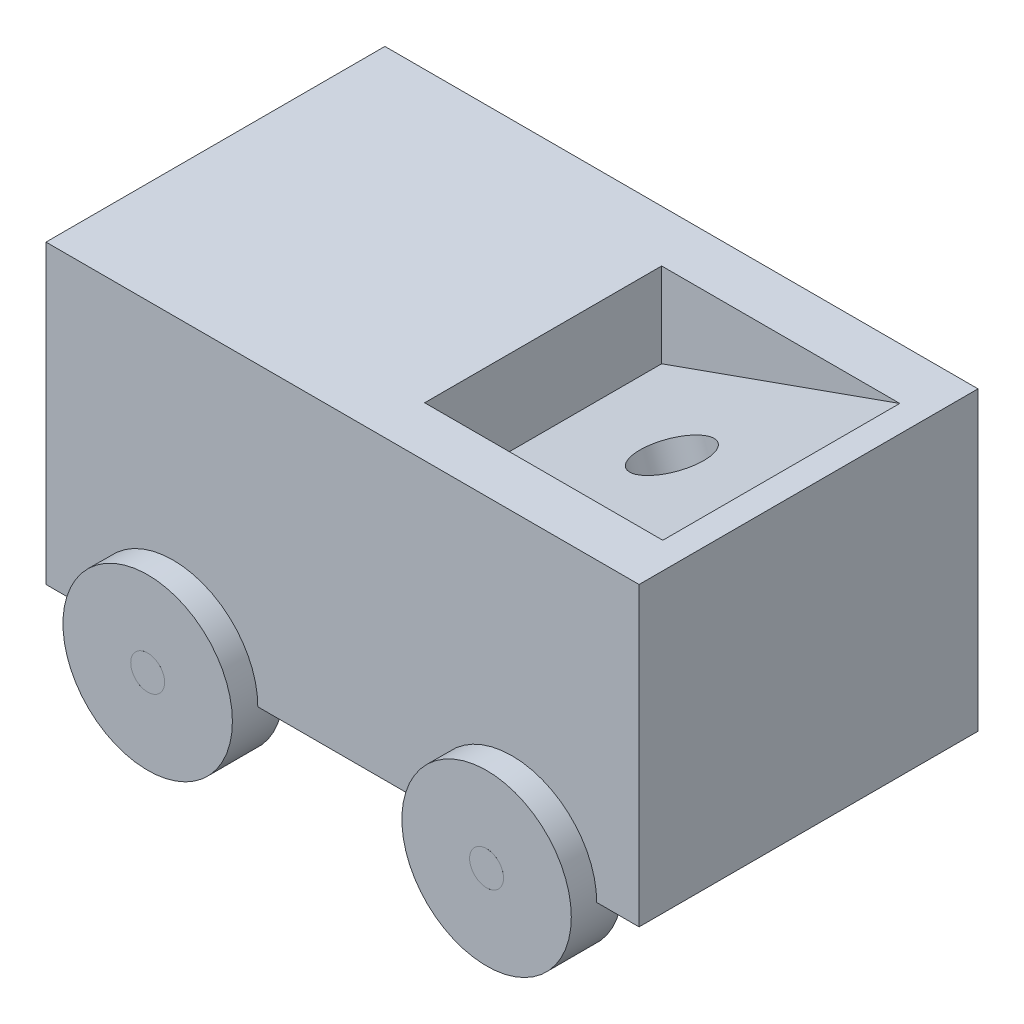
SolidWorks part; units mm, degrees
ref_plane "Front Plane" through (0, 0, 0) normal (0, 0, 1) x (1, 0, 0)
ref_plane "Top Plane" through (0, 0, 0) normal (0, 1, 0) x (1, 0, 0)
ref_plane "Right Plane" through (0, 0, 0) normal (1, 0, 0) x (0, 0, -1)
sketch "Sketch2" plane through (0, 0, 0) normal (0, 0, 1) x (1, 0, 0)
  line L1 (0, 0) -> (-70, 0)
  line L2 (0, 0) -> (0, -35)
  line L3 (0, -35) -> (-70, -35)
  line L4 (-70, 0) -> (-70, -35)
extrude "Boss-Extrude2" add sketch "Sketch2" along normal blind 40
sketch "Sketch3" plane through (0, 0, 0) normal (0, 1, 0) x (1, 0, 0)
  line L1 (-31.2286, -34.0804) -> (-3.1227, -34.0804)
  line L2 (-31.2286, -34.0804) -> (-31.2286, -6.1085)
  line L3 (-31.2286, -6.1085) -> (-3.1227, -6.1085)
  line L4 (-3.1227, -34.0804) -> (-3.1227, -6.1085)
extrude "Cut-Extrude1" cut sketch "Sketch3" against normal blind 10
sketch "Sketch4" plane through (0, 0, 40) normal (0, 0, 1) x (1, 0, 0)
  circle A2 centre (-15, -35) radius 10
  circle A4 centre (-55, -35) radius 10
extrude "Cut-Extrude2" cut sketch "Sketch4" against normal blind 3
sketch "Sketch5" plane through (0, 0, 0) normal (0, 0, -1) x (-1, 0, 0)
  circle A1 centre (15, -35) radius 10
  circle A3 centre (55, -35) radius 10
extrude "Cut-Extrude3" cut sketch "Sketch5" against normal blind 3
sketch "Sketch6" plane through (0, 0, 40) normal (0, 0, 1) x (1, 0, 0)
  circle A0 centre (-55, -35) radius 10
extrude "Boss-Extrude3" add sketch "Sketch6" along normal blind 3 and the other way blind 3
sketch "Sketch7" plane through (0, 0, 3) normal (0, 0, -1) x (-1, 0, 0)
  line L2 (45, -35) -> (65, -35) construction
  circle A2 centre (55, -35) radius 10
extrude "Boss-Extrude5" add sketch "Sketch7" along normal blind 6
sketch "Sketch8" plane through (0, 0, -3) normal (0, 0, -1) x (-1, 0, 0)
  circle A1 centre (55, -35) radius 2
extrude "Cut-Extrude5" cut sketch "Sketch8" against normal blind 46
sketch "Sketch9" plane through (0, 0, -3) normal (0, 0, -1) x (-1, 0, 0)
  circle A0 centre (55, -35) radius 2
extrude "Boss-Extrude8" add sketch "Sketch9" along normal blind 0.0001 and the other way blind 46.0001 contours A0
sketch "Sketch10" plane through (0, 0, 40) normal (0, 0, 1) x (1, 0, 0)
  circle A0 centre (-15, -35) radius 10
extrude "Boss-Extrude9" add sketch "Sketch10" along normal blind 3 and the other way blind 3
sketch "Sketch11" plane through (0, 0, 0) normal (0, 0, -1) x (-1, 0, 0)
  circle A0 centre (15, -35) radius 10
extrude "Boss-Extrude10" add sketch "Sketch11" along normal blind 3 and the other way blind 3
sketch "Sketch12" plane through (0, 0, -3) normal (0, 0, -1) x (-1, 0, 0)
  circle A1 centre (15, -35) radius 2
extrude "Cut-Extrude6" cut sketch "Sketch12" against normal blind 46
sketch "Sketch13" plane through (0, 0, -3) normal (0, 0, -1) x (-1, 0, 0)
  circle A0 centre (15, -35) radius 2
extrude "Boss-Extrude11" add sketch "Sketch13" along normal blind 0.001 and the other way blind 46.001
sketch "Sketch14" plane through (0, 0, 34.0804) normal (0, 0, -1) x (-1, 0, 0)
  line L0 (3.1227, 0) -> (31.2286, -10)
  line L1 (31.2286, -10) -> (3.1227, -10) construction
  line L2 (31.2286, -10) -> (3.1227, -10)
  line L3 (3.1227, -10) -> (3.1227, 0)
extrude "Boss-Extrude12" add sketch "Sketch14" along normal blind 28
sketch "Sketch15" plane through (-0.3509, 0.9862, 0) normal (-0.3352, 0.9421, 0) x (0.9421, 0.3352, 0)
  circle A0 centre (-15.8401, -21.5019) radius 4
sketch "Sketch16" plane through (-0.3509, 0.9862, 0) normal (-0.3352, 0.9421, 0) x (0.9421, 0.3352, 0)
  circle A0 centre (-16.3743, -20.3525) radius 4
sketch "Sketch18" plane through (-0.3509, 0.9862, 0) normal (-0.3352, 0.9421, 0) x (0.9421, 0.3352, 0)
  circle A1 centre (-16.3743, -20.3525) radius 4
extrude "Cut-Extrude11" cut sketch "Sketch18" against normal blind 10
sketch "Sketch19" plane through (-70, 0, 0) normal (-1, 0, 0) x (0, 0, 1)
  circle A0 centre (20, -5.5) radius 5.5
extrude "Boss-Extrude13" add sketch "Sketch19" along normal blind 0.001
